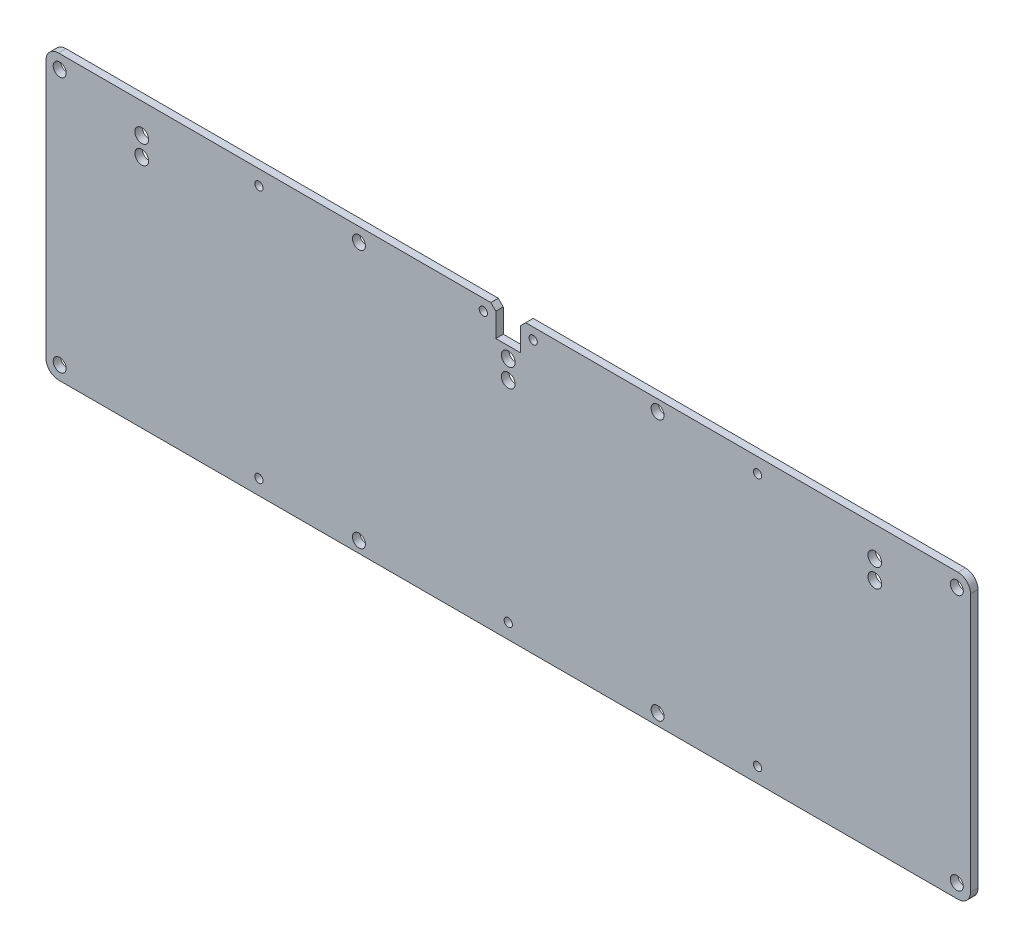
SolidWorks part; units mm, degrees
ref_plane "Front Plane" through (0, 0, 0) normal (0, 0, 1) x (1, 0, 0)
ref_plane "Top Plane" through (0, 0, 0) normal (0, 1, 0) x (1, 0, 0)
ref_plane "Right Plane" through (0, 0, 0) normal (1, 0, 0) x (0, 0, -1)
sketch "Model" plane through (0, 0, 0) normal (0, 0, 1) x (1, 0, 0)
  line L0 (0, 108.6) -> (0, 5)
  line L1 (365.775, 0) -> (5, 0)
  line L2 (370.775, 108.6) -> (370.775, 5)
  line L3 (180.3875, 111.6) -> (178.3875, 113.6)
  line L4 (5, 113.6) -> (178.3875, 113.6)
  line L5 (180.3875, 111.6) -> (180.3875, 102.1)
  line L6 (180.3875, 102.1) -> (190.3875, 102.1)
  line L7 (190.3875, 111.6) -> (192.3875, 113.6)
  line L8 (190.3875, 111.6) -> (190.3875, 102.1)
  line L9 (192.3875, 113.6) -> (365.775, 113.6)
  arc A0 (365.775, 0) -> (370.775, 5) centre (365.775, 5) ccw
  arc A1 (370.775, 108.6) -> (365.775, 113.6) centre (365.775, 108.6) ccw
  arc A2 (0, 5) -> (5, 0) centre (5, 5) ccw
  circle A3 centre (5.5, 108.1) radius 2.6
  circle A4 centre (5.5, 5.5) radius 2.6
  circle A5 centre (365.275, 5.5) radius 2.6
  circle A6 centre (365.275, 108.1) radius 2.6
  arc A7 (5, 113.6) -> (0, 108.6) centre (5, 108.6) ccw
  circle A8 centre (125.5, 4.5) radius 2.6
  circle A9 centre (195.3875, 109.1) radius 1.65
  circle A10 centre (175.3875, 109.1) radius 1.65
  circle A11 centre (38.3875, 94.1) radius 2.75
  circle A12 centre (38.3875, 101.6) radius 2.75
  circle A13 centre (332.3875, 94.1) radius 2.75
  circle A14 centre (332.3875, 101.6) radius 2.75
  circle A15 centre (185.3875, 90.1) radius 2.75
  circle A16 centre (185.3875, 97.6) radius 2.75
  circle A17 centre (85.3875, 107.6) radius 1.65
  circle A18 centre (285.3875, 107.6) radius 1.65
  circle A19 centre (85.3875, 6) radius 1.65
  circle A20 centre (185.3875, 6) radius 1.65
  circle A21 centre (285.3875, 6) radius 1.65
  circle A22 centre (245.275, 4.5) radius 2.6
  circle A23 centre (125.5, 108.1) radius 2.6
  circle A24 centre (245.275, 109.1) radius 2.6
  point P60 (180.3875, 106.85)
  dimension "D2" = 3.3
  dimension "D3" = 3.3
  dimension "D4" = 3.3
  dimension "D5" = 3.3
  dimension "D6" = 3.3
  dimension "D7" = 3.3
  dimension "D8" = 3.3
  dimension "D20" = 5.2
  dimension "D21" = 5.5
  dimension "D1" = 113.6
  dimension "D9" = 5.5
  dimension "D10" = 5.5
  dimension "D11" = 10
  dimension "D14" = 7.5
  dimension "D15" = 11.5
  dimension "D12" = 59.8875
  dimension "D16" = 38.3875
  dimension "D17" = 85.3875
  dimension "D18" = 120
  dimension "D19" = 119.775
  dimension "D13" = 4.5
  dimension "D22" = 6
  dimension "D23" = 5.5
extrude "Boss-Extrude1" add sketch "Model" along normal blind 3
equation "\"A\"= 3.3"
equation "\"D2@Model\"=\"A\""
equation "\"D3@Model\"=\"A\""
equation "\"D4@Model\"=\"A\""
equation "\"D5@Model\"=\"A\""
equation "\"D6@Model\"=\"A\""
equation "\"D7@Model\"=\"A\""
equation "\"D8@Model\"=\"A\""
